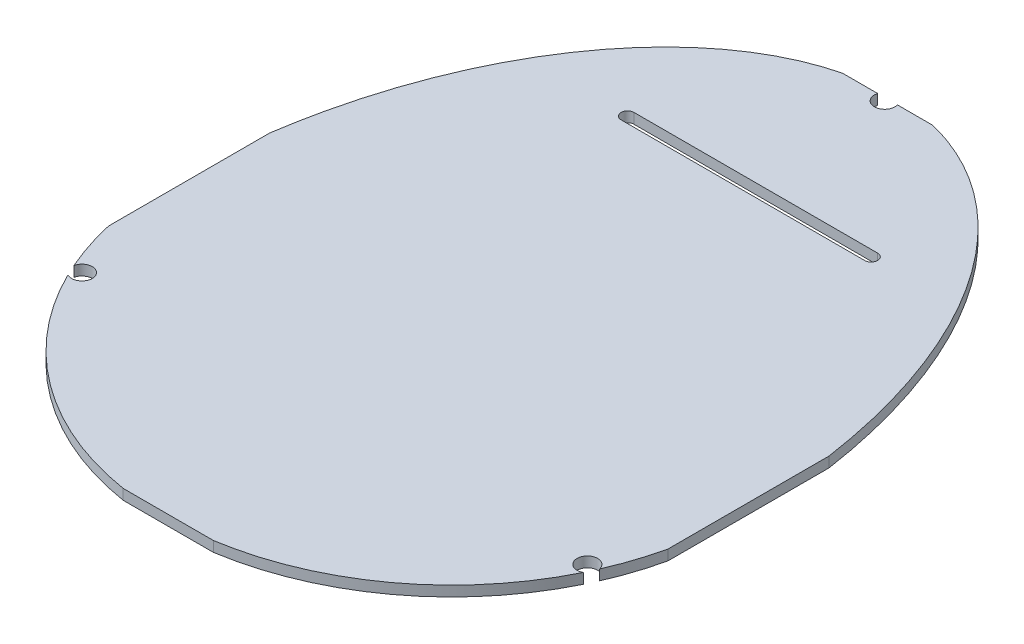
SolidWorks part; units mm, degrees
ref_plane "Front Plane" through (0, 0, 0) normal (0, 0, 1) x (1, 0, 0)
ref_plane "Top Plane" through (0, 0, 0) normal (0, 1, 0) x (1, 0, 0)
ref_plane "Right Plane" through (0, 0, 0) normal (1, 0, 0) x (0, 0, -1)
sketch "Sketch1" plane through (0, 0, 0) normal (0, 1, 0) x (1, 0, 0)
  line L0 (-3.5, 32.4962) -> (3.5, 32.4962)
  line L1 (-21.6986, 6.25) -> (-21.6986, -6.25)
  line L2 (-3.5, -23.3004) -> (3.5, -23.3004)
  line L3 (21.6986, 6.25) -> (21.6986, -6.25)
  line L4 (-21.6986, 0) -> (0, 0) construction
  line L5 (0, 0) -> (21.6986, 0) construction
  line L6 (0, 32.4962) -> (0, -23.3004) construction
  arc A0 (-21.6986, -6.25) -> (-3.5, -23.3004) centre (0, -1.3274) ccw
  arc A1 (21.6986, -6.25) -> (3.5, -23.3004) centre (0, -1.3274) cw
  arc A2 (21.6986, -6.25) -> (22.25, -1.3274) centre (0, -1.3274) ccw construction
  ellipse E0 centre (0, -1.3274) end of major axis (0, -35.5774) minor radius 22.25
  dimension "D3" = 34.25
  dimension "D4" = 22.25
  dimension "D1" = 12.5
  dimension "D2" = 7
extrude "Boss-Extrude1" add sketch "Sketch1" along normal blind 0.8 contours L3 E0 L0 L1 A0 L2 A1
sketch "Sketch2" plane through (0, 0, 0) normal (0, -1, 0) x (1, 0, 0)
  line L0 (-8.95, -21.2726) -> (9.95, -21.2726) construction
  line L1 (-8.95, -20.7726) -> (9.95, -20.7726)
  line L2 (-8.95, -21.7726) -> (9.95, -21.7726)
  line L3 (9.95, -15.7037) -> (9.95, -19.1511) construction
  line L4 (-8.95, -19.1613) -> (-8.95, -15.7037) construction
  line L7 (-16.9, -20.7726) -> (16.9, -20.7726) construction
  arc A0 (-8.95, -20.7726) -> (-8.95, -21.7726) centre (-8.95, -21.2726) ccw
  arc A1 (9.95, -21.7726) -> (9.95, -20.7726) centre (9.95, -21.2726) ccw
  point P2 (0.5, -21.2726)
  dimension "D1" = 1
extrude "Cut-Extrude1" cut sketch "Sketch2" against normal through all
sketch "Sketch3" plane through (0, 0.8, 0) normal (0, 1, 0) x (1, 0, 0)
  line L0 (-19.6034, -10.3974) -> (0, -10.3974) construction
  line L1 (0, -10.3974) -> (19.6034, -10.3974) construction
  line L2 (-3.5, -23.3004) -> (3.5, -23.3004) construction
  circle A0 centre (0, 32.2725) radius 0.8
  circle A1 centre (19.6034, -10.3974) radius 0.8
  circle A2 centre (-19.6034, -10.3974) radius 0.8
  dimension "D1" = 1.6
  dimension "D2" = 55.5729
  dimension "D3" = 39.2069
  dimension "D4" = 12.903
extrude "Cut-Extrude2" cut sketch "Sketch3" against normal through all
